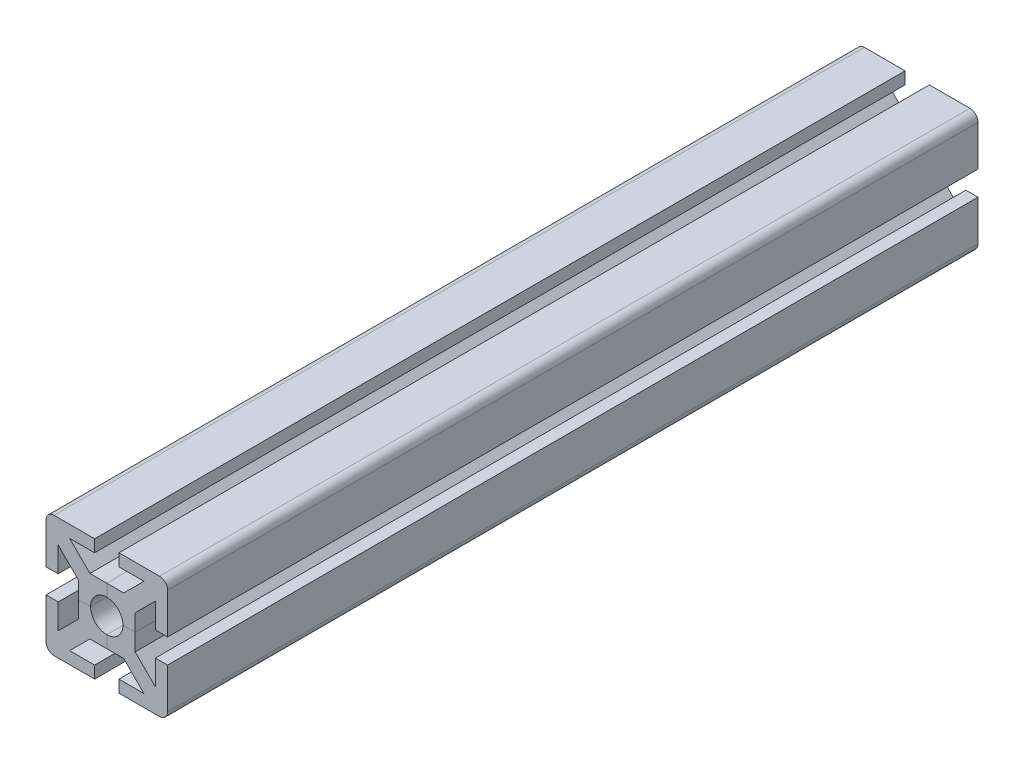
SolidWorks part; units mm, degrees
ref_plane "Alzado" through (0, 0, 0) normal (0, 0, 1) x (1, 0, 0)
ref_plane "Planta" through (0, 0, 0) normal (0, 1, 0) x (1, 0, 0)
ref_plane "Vista lateral" through (0, 0, 0) normal (1, 0, 0) x (0, 0, -1)
sketch "Croquis1" plane through (0, 0, 0) normal (0, 0, 1) x (1, 0, 0)
  line L0 (0, 0) -> (50000, 0) construction
  line L1 (-15, 15) -> (15, 15) construction
  line L2 (-15, 15) -> (-15, -15) construction
  line L3 (-15, -15) -> (15, -15) construction
  line L4 (15, 15) -> (15, -15) construction
  line L5 (-15, 15) -> (15, -15) construction
  line L6 (-15, -15) -> (15, 15) construction
  line L7 (0, 0) -> (0, -50000) construction
  line L8 (0, 4) -> (0, 7)
  line L9 (0, 7) -> (4.1716, 7)
  line L10 (4.1716, 7) -> (9.1716, 12)
  line L11 (9.1716, 12) -> (3, 12)
  line L12 (3, 12) -> (3, 15)
  line L13 (3, 15) -> (15, 15)
  line L20 (2.8284, 2.8284) -> (15, 15)
  arc A0 (2.8284, 2.8284) -> (0, 4) centre (0, 0) ccw
  point P0 (0, 0)
  dimension "D3" = 4
  dimension "D1" = 30
  dimension "D2" = 6
  dimension "D4" = 8
  dimension "D5" = 3
  dimension "D6" = 2
extrude "Saliente-Extruir1" add sketch "Croquis1" along normal mid plane 200
mirror "Simetría1" about plane through (2.8284, 2.8284, 100) normal (-0.7071, 0.7071, 0) of "Saliente-Extruir1"
fillet "Redondeo1" radius 2 1 edges at (15, 15, 0)
pattern_circular "MatrizC4" count 4 over 360 about axis through (0, 0, 0) along (0, 0, 1) of bodies 102
